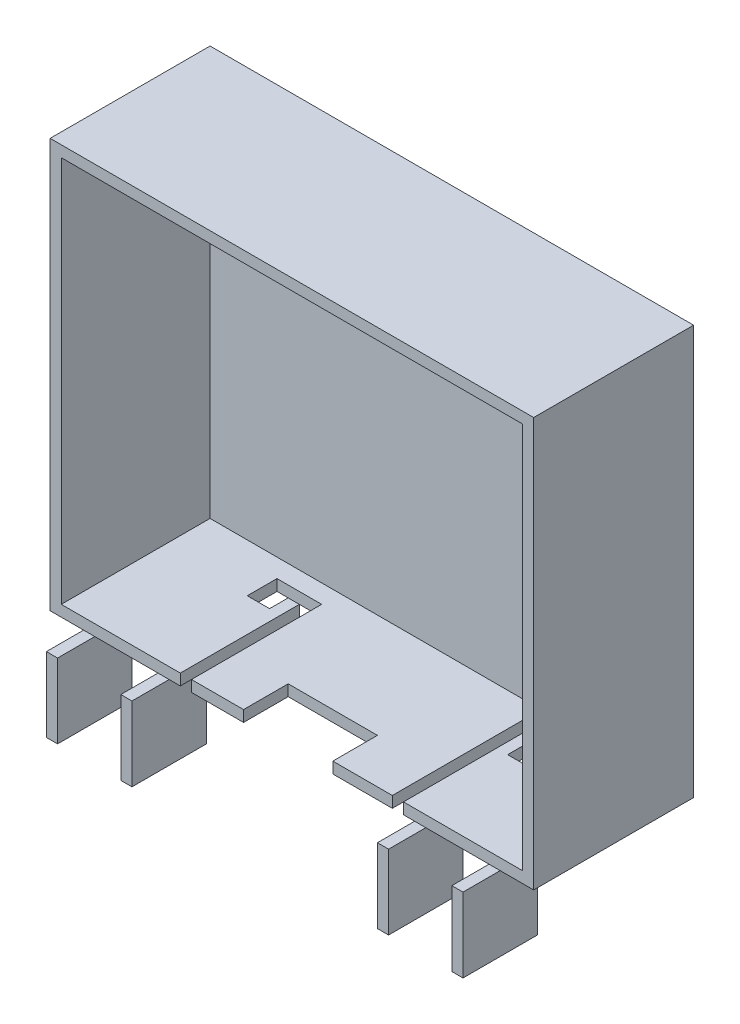
SolidWorks part; units mm, degrees
ref_plane "前视基准面" through (0, 0, 0) normal (0, 0, 1) x (1, 0, 0)
ref_plane "上视基准面" through (0, 0, 0) normal (0, 1, 0) x (1, 0, 0)
ref_plane "右视基准面" through (0, 0, 0) normal (1, 0, 0) x (0, 0, -1)
sketch "草图1" plane through (0, 0, 0) normal (0, 0, 1) x (1, 0, 0)
  line L0 (0, 0) -> (65, 0)
  line L1 (65, 0) -> (65, -55)
  line L2 (65, -55) -> (0, -55)
  line L3 (0, -55) -> (0, 0)
extrude "凸台-拉伸1" add sketch "草图1" along normal blind 1.5
sketch "草图2" plane through (0, 0, 1.5) normal (0, 0, 1) x (1, 0, 0)
  line L1 (65, 0) -> (65, -55)
  line L2 (65, -55) -> (0, -55)
  line L3 (0, -55) -> (0, 0)
  line L4 (0, 0) -> (65, 0)
  line L5 (1.5, -53.5) -> (63.5, -53.5)
  line L9 (1.5, -53.5) -> (1.5, -1.5)
  line L10 (63.5, -53.5) -> (63.5, -1.5)
  line L11 (63.5, -1.5) -> (1.5, -1.5)
extrude "凸台-拉伸2" add sketch "草图2" along normal blind 20
sketch "草图3" plane through (0, -55, 0) normal (0, -1, 0) x (1, 0, 0)
  line L0 (38, 15.5) -> (38, 21.5)
  line L1 (26, 15.5) -> (26, 21.5)
  line L2 (26, 21.5) -> (38, 21.5)
  line L7 (0, 21.5) -> (65, 21.5) construction
  line L10 (26, 15.5) -> (38, 15.5)
extrude "切除-拉伸1" cut sketch "草图3" against normal blind 1.5
sketch "草图4" plane through (0, -55, 0) normal (0, -1, 0) x (1, 0, 0)
  line L0 (0, 0) -> (0, 4)
  line L1 (0, 21.5) -> (0, 0) construction
  line L3 (19, 4) -> (19, 21.5)
  line L4 (0, 21.5) -> (26, 21.5) construction
  line L7 (17.5, 5.5) -> (16, 5.5)
  line L11 (13, 4) -> (19, 4)
  line L12 (46, 4) -> (52, 4)
  line L13 (17.5, 5.5) -> (17.5, 21.5)
  line L19 (47.5, 5.5) -> (49, 5.5)
  line L21 (49, 9) -> (52, 9)
  line L23 (0, 21.5) -> (26, 21.5) construction
  line L24 (17.5, 21.5) -> (19, 21.5)
  line L25 (16, 5.5) -> (16, 8)
  line L26 (16, 8) -> (13, 8)
  line L27 (13, 8) -> (13, 4)
  line L28 (52, 9) -> (52, 4)
  line L29 (49, 5.5) -> (49, 9)
  line L30 (47.5, 5.5) -> (47.5, 21.5)
  line L31 (38, 21.5) -> (65, 21.5) construction
  line L32 (46, 4) -> (46, 21.5)
extrude "切除-拉伸2" cut sketch "草图4" against normal blind 1.5
sketch "草图5" plane through (0, -55, 0) normal (0, -1, 0) x (1, 0, 0)
  line L1 (16, 16.5) -> (14.5, 16.5)
  line L4 (14.5, 26.5) -> (16, 26.5)
  line L8 (4.5, 16.5) -> (6, 16.5)
  line L9 (49, 16.5) -> (50.5, 16.5)
  line L14 (50.5, 26.5) -> (50.5, 16.5)
  line L18 (60.5, 16.5) -> (59, 16.5)
  line L19 (49, 26.5) -> (49, 16.5)
  line L20 (4.5, 26.5) -> (6, 26.5)
  line L24 (49, 26.5) -> (50.5, 26.5)
  line L27 (59, 26.5) -> (60.5, 26.5)
  line L28 (60.5, 26.5) -> (60.5, 16.5)
  line L31 (59, 26.5) -> (59, 16.5)
  line L32 (16, 26.5) -> (16, 16.5)
  line L33 (14.5, 26.5) -> (14.5, 16.5)
  line L34 (6, 26.5) -> (6, 16.5)
  line L35 (4.5, 26.5) -> (4.5, 16.5)
extrude "凸台-拉伸3" add sketch "草图5" along normal blind 10
